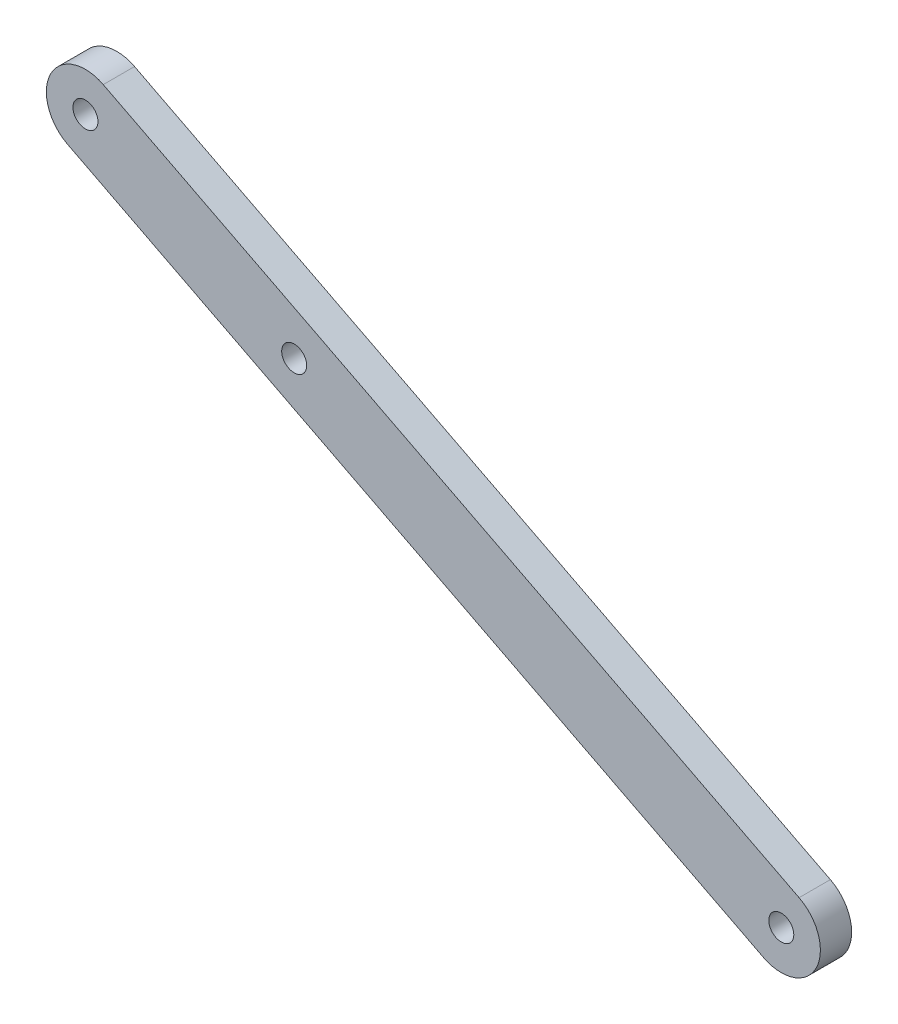
SolidWorks part; units mm, degrees
ref_plane "Front Plane" through (0, 0, 0) normal (0, 0, 1) x (1, 0, 0)
ref_plane "Top Plane" through (0, 0, 0) normal (0, 1, 0) x (1, 0, 0)
ref_plane "Right Plane" through (0, 0, 0) normal (1, 0, 0) x (0, 0, -1)
sketch "Sketch1" plane through (0, 0, 0) normal (0, 0, 1) x (1, 0, 0)
  line L0 (0, 0) -> (-89.0137, 45.5692) construction
  line L1 (-2.2785, -4.4507) -> (-91.2922, 41.1186)
  line L2 (2.2785, 4.4507) -> (-86.7353, 50.0199)
  arc A0 (-2.2785, -4.4507) -> (2.2785, 4.4507) centre (0, 0) ccw
  arc A1 (-86.7353, 50.0199) -> (-91.2922, 41.1186) centre (-89.0137, 45.5692) ccw
  circle A2 centre (-89.0137, 45.5692) radius 1.6
  circle A3 centre (0, 0) radius 1.6
  circle A5 centre (-62.3096, 31.8985) radius 1.6
  point P3 (-44.5069, 22.7846)
  point P14 (-26.7041, 13.6708)
  dimension "D3" = 3.2
  dimension "D1" = 10
  dimension "D2" = 100
  dimension "D4" = 30
extrude "Boss-Extrude1" add sketch "Sketch1" along normal blind 4
